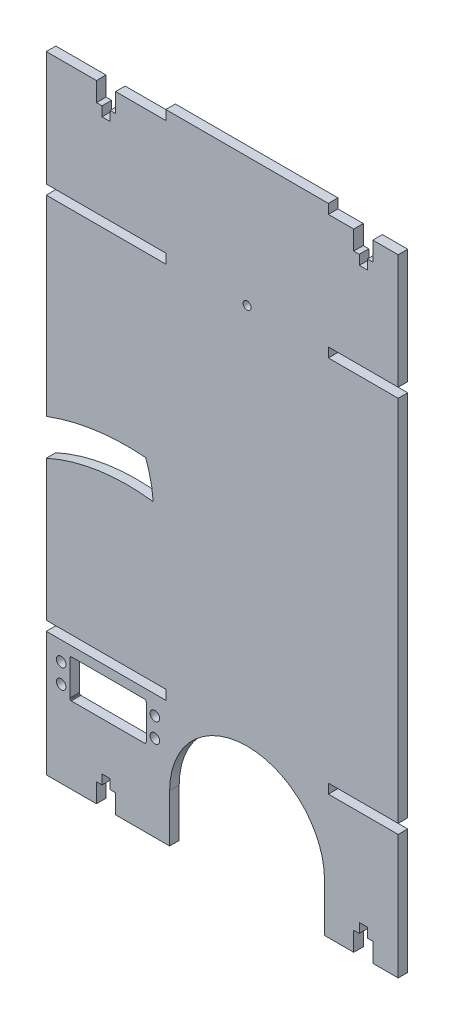
SolidWorks part; units mm, degrees
ref_plane "Front Plane" through (0, 0, 0) normal (0, 0, 1) x (1, 0, 0)
ref_plane "Top Plane" through (0, 0, 0) normal (0, 1, 0) x (1, 0, 0)
ref_plane "Right Plane" through (0, 0, 0) normal (1, 0, 0) x (0, 0, -1)
sketch "Sketch2" plane through (0, 0, 0) normal (0, 0, 1) x (1, 0, 0)
  line L1 (-92, 166.25) -> (92, 166.25)
  line L2 (-92, 166.25) -> (-92, -166.25)
  line L3 (-92, -166.25) -> (92, -166.25)
  line L4 (92, 166.25) -> (92, -166.25)
  line L5 (-92, 166.25) -> (92, -166.25) construction
  line L6 (-92, -166.25) -> (92, 166.25) construction
  point P0 (0, 0)
  dimension "D1" = 332.5
  dimension "D2" = 184
extrude "Boss-Extrude1" add sketch "Sketch2" along normal blind 5
sketch "Sketch3" plane through (0, 0, 5) normal (0, 0, 1) x (1, 0, 0)
  line L0 (-92, 166.25) -> (-92, -166.25) construction
  line L1 (-29.5, -96.25) -> (-92, -96.25)
  line L2 (-29.5, -96.25) -> (-29.5, -101.25)
  line L3 (-29.5, -101.25) -> (-92, -101.25)
  line L4 (-92, -96.25) -> (-92, -101.25)
  line L5 (-29.5, -96.25) -> (-92, -101.25) construction
  line L6 (-29.5, -101.25) -> (-92, -96.25) construction
  line L7 (-92, -101.25) -> (-29.5, -101.25) construction
  line L8 (92, -166.25) -> (92, 166.25) construction
  line L9 (55.5, -96.25) -> (92, -96.25)
  line L10 (55.5, -96.25) -> (55.5, -101.25)
  line L11 (55.5, -101.25) -> (92, -101.25)
  line L12 (92, -96.25) -> (92, -101.25)
  line L13 (55.5, -96.25) -> (92, -101.25) construction
  line L14 (55.5, -101.25) -> (92, -96.25) construction
  line L15 (55.5, -101.25) -> (98, -101.25) construction
  line L16 (-27.5, -141.25) -> (-27.5, -166.25)
  line L17 (-92, -166.25) -> (92, -166.25) construction
  line L18 (-27.5, -166.25) -> (53.5, -166.25)
  line L19 (53.5, -166.25) -> (53.5, -141.25)
  line L20 (-92, 101.25) -> (-29.5, 101.25) construction
  line L21 (-29.5, 161.25) -> (-92, 161.25)
  line L22 (-29.5, 161.25) -> (-29.5, 166.25)
  line L23 (-29.5, 166.25) -> (-92, 166.25)
  line L24 (-92, 161.25) -> (-92, 166.25)
  line L25 (-29.5, 161.25) -> (-92, 166.25) construction
  line L26 (-29.5, 166.25) -> (-92, 161.25) construction
  line L27 (55.5, 161.25) -> (92, 161.25)
  line L28 (55.5, 161.25) -> (55.5, 166.25)
  line L29 (55.5, 166.25) -> (92, 166.25)
  line L30 (92, 161.25) -> (92, 166.25)
  line L31 (55.5, 161.25) -> (92, 166.25) construction
  line L32 (55.5, 166.25) -> (92, 161.25) construction
  line L33 (-29.5, 96.25) -> (-92, 96.25)
  line L34 (-29.5, 96.25) -> (-29.5, 101.25)
  line L35 (-29.5, 101.25) -> (-92, 101.25)
  line L36 (-92, 96.25) -> (-92, 101.25)
  line L37 (-29.5, 96.25) -> (-92, 101.25) construction
  line L38 (-29.5, 101.25) -> (-92, 96.25) construction
  line L39 (55.5, 101.25) -> (98, 101.25) construction
  line L40 (55.5, 96.25) -> (92, 96.25)
  line L41 (55.5, 96.25) -> (55.5, 101.25)
  line L42 (55.5, 101.25) -> (92, 101.25)
  line L43 (92, 96.25) -> (92, 101.25)
  line L44 (55.5, 96.25) -> (92, 101.25) construction
  line L45 (55.5, 101.25) -> (92, 96.25) construction
  arc A0 (53.5, -141.25) -> (-27.5, -141.25) centre (13, -141.25) ccw
  point P4 (-60.75, -98.75)
  point P14 (73.75, -98.75)
  point P32 (-60.75, 163.75)
  point P39 (73.75, 163.75)
  point P46 (-60.75, 98.75)
  point P54 (73.75, 98.75)
extrude "Cut-Extrude2" cut sketch "Sketch3" against normal blind 5
sketch "Sketch4" plane through (0, 0, 5) normal (0, 0, 1) x (1, 0, 0)
  line L0 (-60.75, 161.25) -> (-60.75, 132.1129) construction
  line L1 (-92, 161.25) -> (-29.5, 161.25) construction
  line L2 (13, 166.25) -> (13, 127.9445) construction
  line L3 (55.5, 166.25) -> (-29.5, 166.25) construction
  line L4 (63.681, 161.25) -> (63.681, -166.25) construction
  line L7 (55.5, 161.25) -> (92, 161.25) construction
  line L8 (53.5, -166.25) -> (92, -166.25) construction
  line L9 (63.681, -2.5) -> (78.6939, -2.5) construction
  line L10 (-55.75, 161.25) -> (-55.75, 151.25)
  line L11 (-55.75, 151.25) -> (-58.65, 151.25)
  line L12 (-58.65, 151.25) -> (-58.65, 146.25)
  line L13 (-55.75, 161.25) -> (-65.75, 161.25)
  line L14 (-58.65, 146.25) -> (-62.85, 146.25)
  line L15 (-62.85, 151.25) -> (-62.85, 146.25)
  line L16 (-65.75, 151.25) -> (-62.85, 151.25)
  line L17 (-65.75, 161.25) -> (-65.75, 151.25)
  line L18 (-92, 103.048) -> (92, 103.048) construction
  line L19 (-92, 161.25) -> (-92, 101.25) construction
  line L20 (92, -96.25) -> (92, 96.25) construction
  line L21 (0, 103.048) -> (0, 118.0576) construction
  line L22 (0, 118.0576) -> (13, 118.0576) construction
  line L23 (6.5, 118.0576) -> (6.5, 130.4502) construction
  line L24 (78.75, 161.25) -> (78.75, 151.25)
  line L25 (78.75, 151.25) -> (75.85, 151.25)
  line L26 (75.85, 151.25) -> (75.85, 146.25)
  line L27 (71.65, 146.25) -> (75.85, 146.25)
  line L28 (68.75, 161.25) -> (78.75, 161.25)
  line L29 (71.65, 151.25) -> (71.65, 146.25)
  line L30 (68.75, 151.25) -> (71.65, 151.25)
  line L31 (68.75, 161.25) -> (68.75, 151.25)
  line L32 (68.75, -166.25) -> (68.75, -156.25)
  line L33 (68.75, -156.25) -> (71.65, -156.25)
  line L34 (71.65, -156.25) -> (71.65, -151.25)
  line L35 (68.75, -166.25) -> (78.75, -166.25)
  line L36 (71.65, -151.25) -> (75.85, -151.25)
  line L37 (75.85, -156.25) -> (75.85, -151.25)
  line L38 (78.75, -156.25) -> (75.85, -156.25)
  line L39 (78.75, -166.25) -> (78.75, -156.25)
  line L40 (-65.75, -166.25) -> (-65.75, -156.25)
  line L41 (-65.75, -156.25) -> (-62.85, -156.25)
  line L42 (-62.85, -156.25) -> (-62.85, -151.25)
  line L43 (-58.65, -151.25) -> (-62.85, -151.25)
  line L44 (-55.75, -166.25) -> (-65.75, -166.25)
  line L45 (-58.65, -156.25) -> (-58.65, -151.25)
  line L46 (-55.75, -156.25) -> (-58.65, -156.25)
  line L47 (-55.75, -166.25) -> (-55.75, -156.25)
  point P22 (-60.75, 146.25)
  point P45 (73.75, 146.25)
  point P62 (73.75, -151.25)
  point P63 (-60.75, -151.25)
  dimension "D1" = 10
  dimension "D2" = 2.9
  dimension "D3" = 5
  dimension "D4" = 5
extrude "Cut-Extrude3" cut sketch "Sketch4" against normal blind 10
sketch "Sketch5" plane through (0, 0, 5) normal (0, 0, 1) x (1, 0, 0)
  line L0 (-29.5, 98.75) -> (55.5, 98.75) construction
  line L1 (-29.5, 96.25) -> (-29.5, 101.25) construction
  line L2 (55.5, 96.25) -> (55.5, 101.25) construction
  circle A0 centre (13, 98.75) radius 2.1
  dimension "D1" = 4.2
extrude "Cut-Extrude4" cut sketch "Sketch5" against normal blind 10
sketch "Sketch6" plane through (0, 0, 0) normal (0, 0, -1) x (-1, 0, 0)
  line L0 (40.7, -106.25) -> (40.3997, -106.2962)
  line L1 (40.3997, -106.2962) -> (40.2346, -106.3649)
  line L2 (40.2346, -106.3649) -> (40.0877, -106.4594)
  line L3 (40.0877, -106.4594) -> (39.9929, -106.5429)
  line L4 (39.9929, -106.5429) -> (39.8598, -106.7078)
  line L5 (39.8598, -106.7078) -> (39.7735, -106.8736)
  line L6 (39.7735, -106.8736) -> (39.7239, -107.0327)
  line L7 (39.7239, -107.0327) -> (39.7, -107.25)
  line L8 (39.7, -107.25) -> (39.7, -125.25)
  line L9 (39.7, -125.25) -> (39.8215, -125.7277)
  line L10 (39.8215, -125.7277) -> (39.9929, -125.9571)
  line L11 (39.9929, -125.9571) -> (40.2995, -126.1663)
  line L12 (40.2995, -126.1663) -> (40.7, -126.25)
  line L13 (40.7, -126.25) -> (78.2, -126.25)
  line L14 (78.2, -126.25) -> (78.7, -126.25)
  line L15 (78.7, -126.25) -> (79.0003, -126.2038)
  line L16 (79.0003, -126.2038) -> (79.2841, -126.0617)
  line L17 (79.2841, -126.0617) -> (79.4316, -125.9318)
  line L18 (79.4316, -125.9318) -> (79.6783, -125.4573)
  line L19 (79.6783, -125.4573) -> (79.7, -125.25)
  line L20 (79.7, -125.25) -> (79.7, -107.25)
  line L21 (79.7, -107.25) -> (79.6941, -107.1413)
  line L22 (79.6941, -107.1413) -> (79.6808, -107.0551)
  line L23 (79.6808, -107.0551) -> (79.6548, -106.9527)
  line L24 (79.6548, -106.9527) -> (79.6265, -106.8736)
  line L25 (79.6265, -106.8736) -> (79.5883, -106.7907)
  line L26 (79.5883, -106.7907) -> (79.5402, -106.7078)
  line L27 (79.5402, -106.7078) -> (79.4809, -106.6253)
  line L28 (79.4809, -106.6253) -> (79.4316, -106.5682)
  line L29 (79.4316, -106.5682) -> (79.4071, -106.5429)
  line L30 (79.4071, -106.5429) -> (79.3578, -106.4968)
  line L31 (79.3578, -106.4968) -> (79.2976, -106.4482)
  line L32 (79.2976, -106.4482) -> (79.2286, -106.4011)
  line L33 (79.2286, -106.4011) -> (79.1422, -106.3531)
  line L34 (79.1422, -106.3531) -> (79.0888, -106.3287)
  line L35 (79.0888, -106.3287) -> (79.0003, -106.2962)
  line L36 (79.0003, -106.2962) -> (78.9556, -106.2832)
  line L37 (78.9556, -106.2832) -> (78.8531, -106.2618)
  line L38 (78.8531, -106.2618) -> (78.7551, -106.2515)
  line L39 (78.7551, -106.2515) -> (78.7, -106.25)
  line L40 (78.7, -106.25) -> (40.7, -106.25)
  circle A0 centre (35.2, -111.17) radius 2.5
  circle A1 centre (35.2, -121.33) radius 2.5
  circle A2 centre (84.2, -121.33) radius 2.5
  circle A3 centre (84.2, -111.17) radius 2.5
  arc A4 (40.7, -106.25) -> (39.7, -107.25) centre (40.7, -107.25) ccw construction
  arc A5 (39.7, -125.25) -> (40.7, -126.25) centre (40.7, -125.25) ccw construction
  arc A6 (78.7, -126.25) -> (79.7, -125.25) centre (78.7, -125.25) ccw construction
  arc A7 (79.7, -107.25) -> (78.7, -106.25) centre (78.7, -107.25) ccw construction
extrude "Cut-Extrude5" cut sketch "Sketch6" against normal blind 20
sketch "Sketch7" plane through (0, 0, 0) normal (0, 0, -1) x (-1, 0, 0)
  line L3 (92.154, -4.0107) -> (92, -22.8853)
  line L4 (92, 96.25) -> (92, -96.25) construction
  arc A9 (92.154, -4.0107) -> (39.9761, 3.3554) centre (49.7, -116.25) ccw
  arc A10 (92, -22.8853) -> (36.0805, -14.6589) centre (49.7, -116.25) ccw
  arc A11 (39.9761, 3.3554) -> (36.0805, -14.6589) centre (102.0215, -19.4902) ccw
extrude "Cut-Extrude6" cut sketch "Sketch7" against normal blind 10
